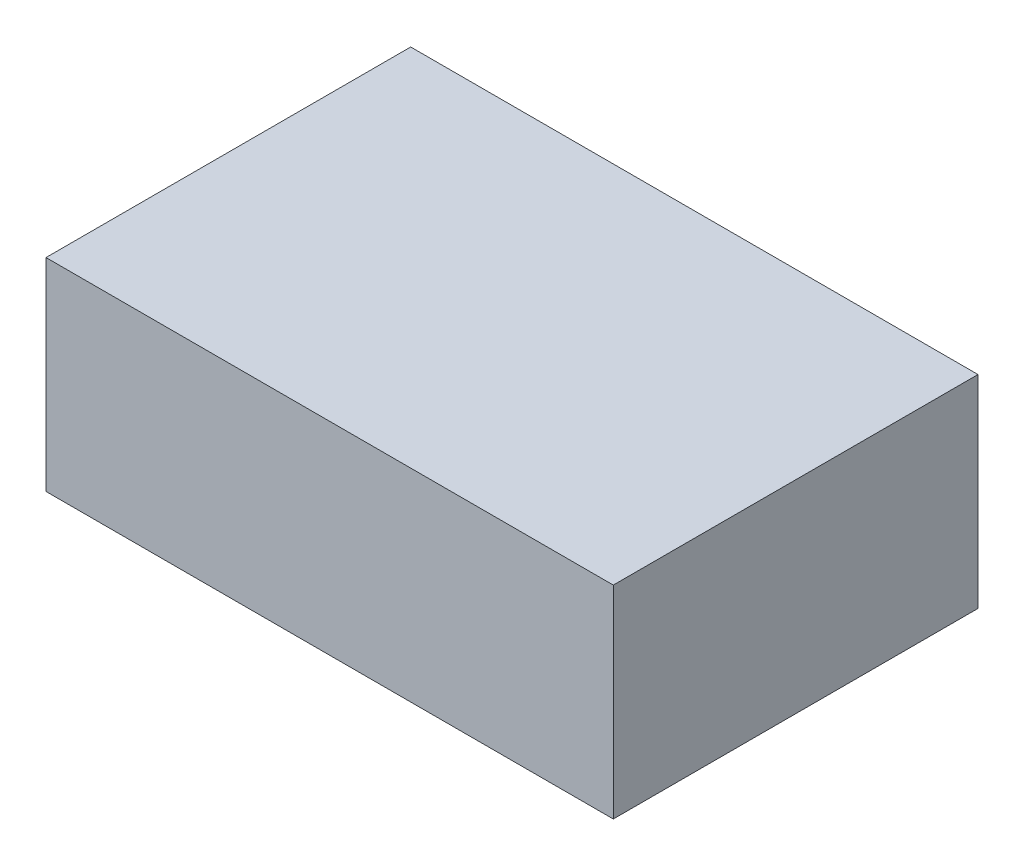
SolidWorks part; units mm, degrees
ref_plane "Front Plane" through (0, 0, 0) normal (0, 0, 1) x (1, 0, 0)
ref_plane "Top Plane" through (0, 0, 0) normal (0, 1, 0) x (1, 0, 0)
ref_plane "Right Plane" through (0, 0, 0) normal (1, 0, 0) x (0, 0, -1)
sketch "Sketch1" plane through (0, 0, 0) normal (0, 1, 0) x (1, 0, 0)
  line L1 (-7, -4.5) -> (7, -4.5)
  line L2 (-7, -4.5) -> (-7, 4.5)
  line L3 (-7, 4.5) -> (7, 4.5)
  line L4 (7, -4.5) -> (7, 4.5)
  line L5 (-7, -4.5) -> (7, 4.5) construction
  line L6 (-7, 4.5) -> (7, -4.5) construction
  point P0 (0, 0)
  dimension "D1" = 14
  dimension "D2" = 9
extrude "Boss-Extrude1" add sketch "Sketch1" along normal blind 5
